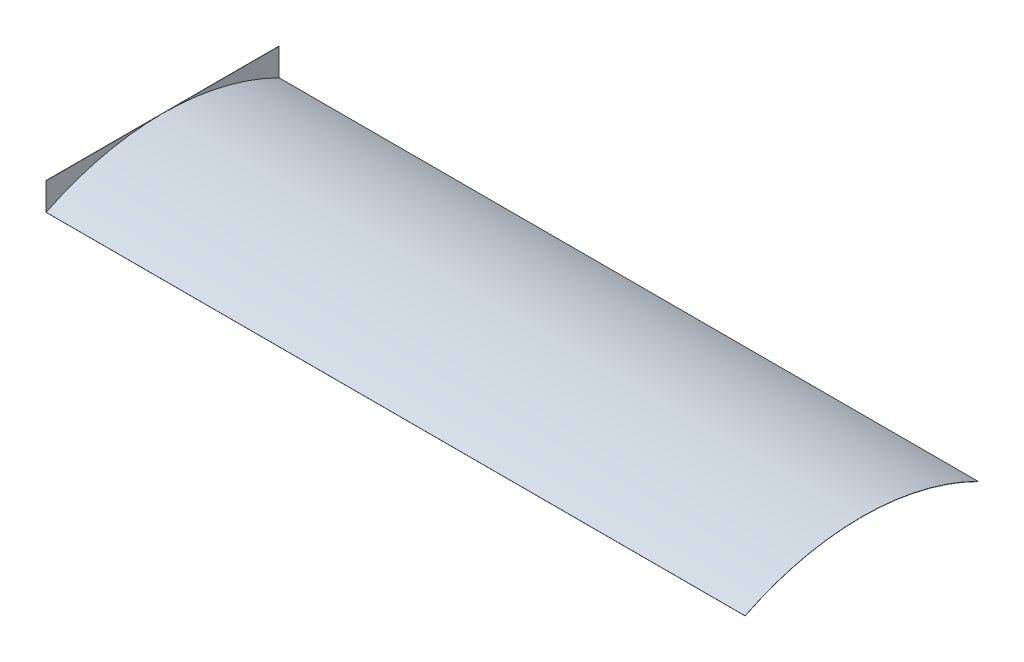
SolidWorks part; units mm, degrees
ref_plane "Front Plane" through (0, 0, 0) normal (0, 0, 1) x (1, 0, 0)
ref_plane "Top Plane" through (0, 0, 0) normal (0, 1, 0) x (1, 0, 0)
ref_plane "Right Plane" through (0, 0, 0) normal (1, 0, 0) x (0, 0, -1)
sketch "Sketch1" plane through (0, 0, 0) normal (0, 1, 0) x (1, 0, 0)
  line L3 (0, -2590.8) -> (0, 0) construction
  line L4 (0, 0) -> (0, -2590.8)
  dimension "D2" = 2590.8
extrude "Extrude-Thin1" add sketch "Sketch1" along normal blind 304.8 thin
sketch "Sketch3" plane through (0, 0, 0) normal (1, 0, 0) x (0, 0, -1)
  arc A0 (-2590.8, 0) -> (0, 0) centre (-1295.4, -2600.325) cw
extrude "Extrude-Thin2" add sketch "Sketch3" along normal blind 7772.4 thin
